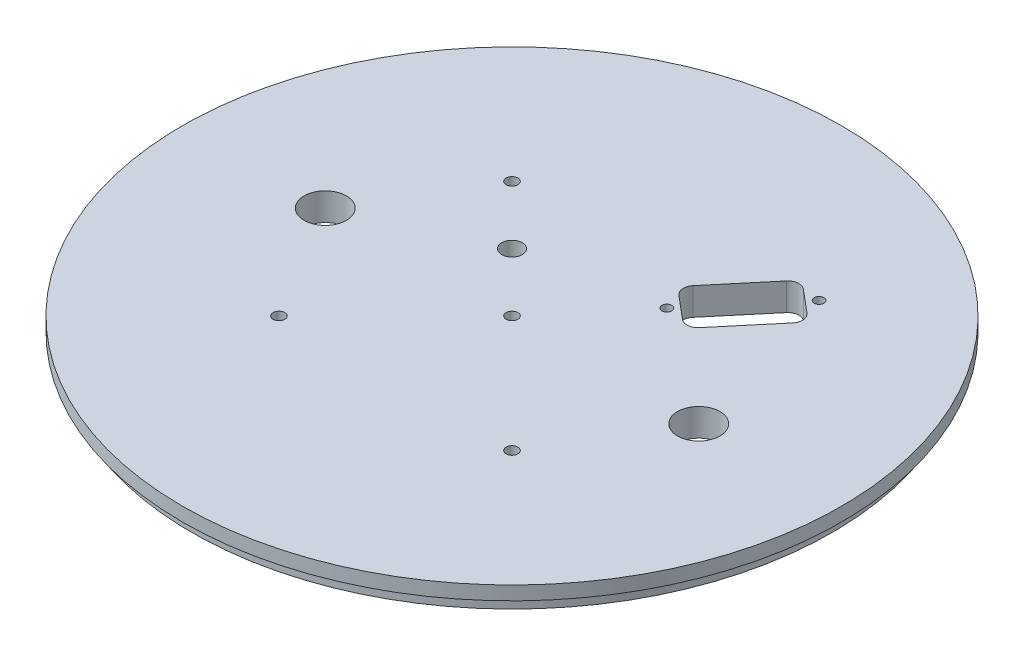
SolidWorks part; units mm, degrees
material "6061-T6 (SS)"
ref_plane "Front Plane" through (0, 0, 0) normal (0, 0, 1) x (1, 0, 0)
ref_plane "Top Plane" through (0, 0, 0) normal (0, 1, 0) x (1, 0, 0)
ref_plane "Right Plane" through (0, 0, 0) normal (1, 0, 0) x (0, 0, -1)
sketch "Sketch1" plane through (0, 0, 0) normal (0, 1, 0) x (1, 0, 0)
  line L0 (0, -76.2) -> (0, 76.2) construction
  line L1 (-76.2, 0) -> (76.2, 0) construction
  line L2 (-26.9408, 26.9408) -> (0, 0) construction
  line L3 (0, 56.7387) -> (0, 29.6936) construction
  line L4 (3.6407, 56.7387) -> (3.6407, 29.6936) construction
  line L5 (-3.6407, 56.7387) -> (-3.6407, 29.6936) construction
  line L6 (0, -56.7387) -> (0, -29.6936) construction
  line L7 (3.6407, -56.7387) -> (3.6407, -29.6936) construction
  line L8 (-3.6407, -56.7387) -> (-3.6407, -29.6936) construction
  line L9 (-53.8815, -53.8815) -> (54.3236, 54.3236) construction
  line L10 (-26.9408, -26.9408) -> (0, 0) construction
  circle A0 centre (0, 0) radius 76.2
  circle A1 centre (0, 0) radius 3.175 construction
  circle A2 centre (43.18, 0) radius 4.9022
  circle A3 centre (-43.18, 0) radius 4.9022
  circle A4 centre (-26.9408, 26.9408) radius 1.3589
  arc A6 (3.6407, 56.7387) -> (-3.6407, 56.7387) centre (0, 56.7387) ccw construction
  arc A7 (-3.6407, 29.6936) -> (3.6407, 29.6936) centre (0, 29.6936) ccw construction
  arc A8 (3.6407, -56.7387) -> (-3.6407, -56.7387) centre (0, -56.7387) cw construction
  arc A9 (-3.6407, -29.6936) -> (3.6407, -29.6936) centre (0, -29.6936) cw construction
  circle A10 centre (26.9408, -26.9408) radius 1.3589
  circle A11 centre (-13.4704, 13.4704) radius 2.3813
  circle A13 centre (-26.9408, -26.9408) radius 1.3589
  circle A14 centre (0, 0) radius 38.1 construction
  circle A15 centre (0, 0) radius 1.3589
  point P16 (0, 43.2162)
  point P19 (0, 0)
  point P26 (0, -43.2162)
  dimension "D1" = 152.4
  dimension "D2" = 6.35
  dimension "D3" = 9.8044
  dimension "D5" = 2.7178
  dimension "D8" = 4.7625
  dimension "D10" = 2.7178
  dimension "D12" = 2.7178
  dimension "D6" = 38.1
  dimension "D7" = 45
  dimension "D4" = 45
  dimension "D9" = 43.18
  dimension "D11" = 38.1
extrude "Boss-Extrude1" add sketch "Sketch1" along normal blind 6.35
sketch "Sketch2" plane through (0, 0, 0) normal (0, -1, 0) x (1, 0, 0)
  circle A0 centre (0, 0) radius 76.2
  circle A1 centre (0, 0) radius 74.041
  dimension "D1" = 152.4
  dimension "D2" = 148.082
extrude "Cut-Extrude1" cut sketch "Sketch2" against normal blind 3.175
sketch "Sketch3" plane through (0, 6.35, 0) normal (0, 1, 0) x (1, 0, 0)
  line L0 (0, 76.2) -> (0, -76.2) construction
  line L1 (-76.2, 0) -> (76.2, 0) construction
  line L2 (0, 34.798) -> (0, 13.97) construction
  line L3 (3.2385, 34.798) -> (3.2385, 13.97)
  line L4 (-3.2385, 34.798) -> (-3.2385, 13.97)
  line L5 (0, -34.798) -> (0, -13.97) construction
  line L6 (3.2385, -34.798) -> (3.2385, -13.97)
  line L7 (-3.2385, -34.798) -> (-3.2385, -13.97)
  circle A0 centre (0, 0) radius 76.2 construction
  arc A1 (3.2385, 34.798) -> (-3.2385, 34.798) centre (0, 34.798) ccw
  arc A2 (-3.2385, 13.97) -> (3.2385, 13.97) centre (0, 13.97) ccw
  arc A3 (3.2385, -34.798) -> (-3.2385, -34.798) centre (0, -34.798) cw
  arc A4 (-3.2385, -13.97) -> (3.2385, -13.97) centre (0, -13.97) cw
  point P7 (0, 13.97)
  point P8 (0, 34.798)
  point P12 (0, 24.384)
  point P20 (0, -24.384)
  point P25 (0, -34.798)
  point P26 (0, -13.97)
  dimension "D1" = 13.97
  dimension "D2" = 20.828
  dimension "D3" = 6.477
extrude "Cut-Extrude2" cut sketch "Sketch3" against normal blind 3.556 from offset 3.175 offset against normal yes
hole_wizard "Tap Drill for #4-40 Tap1" positions "Sketch5" profile "Sketch6" hole size "#4-40" standard "ANSI Inch" end condition through all
sketch "Sketch5" plane through (0, 6.35, 0) normal (0, 1, 0) x (1, 0, 0)
  line L0 (0, 0) -> (53.6567, 63.9455) construction
  line L2 (0, 0) -> (43.18, 0) construction
  point P0 (16.3268, 19.4575)
  point P2 (32.3965, 38.6086)
  dimension "D1" = 50
  dimension "D2" = 25
  dimension "D3" = 25.4
sketch "Sketch6" plane through (16.3268, 6.35, -19.4575) normal (1, 0, 0) x (0, 0, 1)
  line L0 (0, 0) -> (0, 6.35)
  line L1 (0, 6.35) -> (1.1303, 6.35)
  line L2 (1.1303, 6.35) -> (1.1303, 0)
  line L5 (1.1303, 0) -> (0, 0)
  line L11 (0, -6.35) -> (0, 107.95) construction
  dimension "Thru Hole Dia." = 2.2606
  dimension "Thru Hole Depth" = 6.35
sketch "Sketch4" plane through (0, 6.35, 0) normal (0, 1, 0) x (1, 0, 0)
  line L0 (15.1695, 23.4128) -> (20.423, 19.0046)
  line L1 (14.8564, 26.9913) -> (24.7219, 38.7485)
  line L2 (24.0014, 19.3177) -> (33.8669, 31.0749)
  line L3 (28.3003, 39.0616) -> (33.5538, 34.6533)
  line L4 (0, 0) -> (32.3965, 38.6086) construction
  circle A1 centre (16.3268, 19.4575) radius 1.1303 construction
  arc A2 (24.7219, 38.7485) -> (28.3003, 39.0616) centre (26.6676, 37.1158) cw
  arc A3 (33.8669, 31.0749) -> (33.5538, 34.6533) centre (31.9212, 32.7076) ccw
  arc A4 (20.423, 19.0046) -> (24.0014, 19.3177) centre (22.0557, 20.9503) ccw
  arc A5 (14.8564, 26.9913) -> (15.1695, 23.4128) centre (16.8021, 25.3586) ccw
  point P11 (17.7962, 21.2087)
  dimension "D4" = 2.54
  dimension "D1" = 2.286
  dimension "D2" = 2.286
  dimension "D3" = 11.938
extrude "Cut-Extrude3" cut sketch "Sketch4" against normal through all
equation "\"leadDist\"=1.5"
equation "\"Lead_Screw_Dist\" = 3.4in"
equation "\"D9@Sketch1\"=\"Lead_Screw_Dist\"/2"
equation "\"Lead_Screw_Diam\" = 0.386in"
equation "\"D3@Sketch1\"=\"Lead_Screw_Diam\""
equation "\"Bodytube_OD\" = 6.17in"
equation "\"Bodytube_ID\" = 5.998in"
equation "\"Motor_OD\" = 4in"
equation "\"Fwd_Tube_Length\" = 38.5in"
equation "\"Mid_Tube_Length\"= 1in"
equation "\"Aft_Section_Length\"= 36in"
equation "\"AB_Coupler_OD_Length\"= 1in"
equation "\"AB_Coupling_Section_Length\"= 0.375in"
equation "\"AB_Coupler_Length\"= \"AB_Coupler_OD_Length\" + \"AB_Coupling_Section_Length\" * 2"
equation "\"Cutout_Angle\" = 80"
equation "\"AB_Paddle_Height\" = 0.375in"
equation "\"AB_Coupler_Num_Screws\"= 4"
equation "\"Num_Cutouts\" = 3"
equation "\"AB_Coupler_OD\"= 6.17in"
equation "\"AB_Coupler_ID\"= 5.75in"
equation "\"AB_Coupler_Surface_Diameter\"= 5.998in"
equation "\"AB_Coupling_Screw_Diameter\"= 0.15748in"
equation "\"AB_Central_Bushing_Length\" = .4724in"
equation "\"Lead_Screw_Length\" = (\"Mid_Coupler_Length\" + 2*0.375in + 2*.75in)"
equation "\"Paddle_Pin_Offset\" = .25in"
equation "\"Paddle_Pin_Radius\" = 2.25in"
equation "\"SS_Paddle_Pin_Radius\" = 2.25*0.66in"
equation "\"Paddle_Gear_OD\" = 3.2in"
equation "\"Drive_Gear_OD\" = 1.7in"
equation "\"Fwd_BKHD_From_Top\" = 18in"
equation "\"Fin_Thickness\"= .118in"
equation "\"Guiderail_Cutout_Diameter\"= 1.5in"
equation "\"DB9_Hole_Dist\" = 25mm"
equation "\"Airbrakes_Wire_Hole_Dia\" = .25in"
equation "\"Airbrakes_Wire_Hole_Dist\" = 1.1in"
equation "\"Servo_Gear_Offset\" = 0.5in"
equation "\"Mid_Coupler_Length\" = 13in"
equation "\"D2@Sketch5\"=\"DB9_Hole_Dist\""
equation "\"DB9_Relief_Width\" = 0.47in"
equation "\"DB9_Relief_Hole_Offset\" = 0.09in"
equation "\"D1@Sketch4\"=\"DB9_Relief_Hole_Offset\""
equation "\"D2@Sketch4\"=\"DB9_Relief_Hole_Offset\""
equation "\"D3@Sketch4\"=\"DB9_Relief_Width\""
